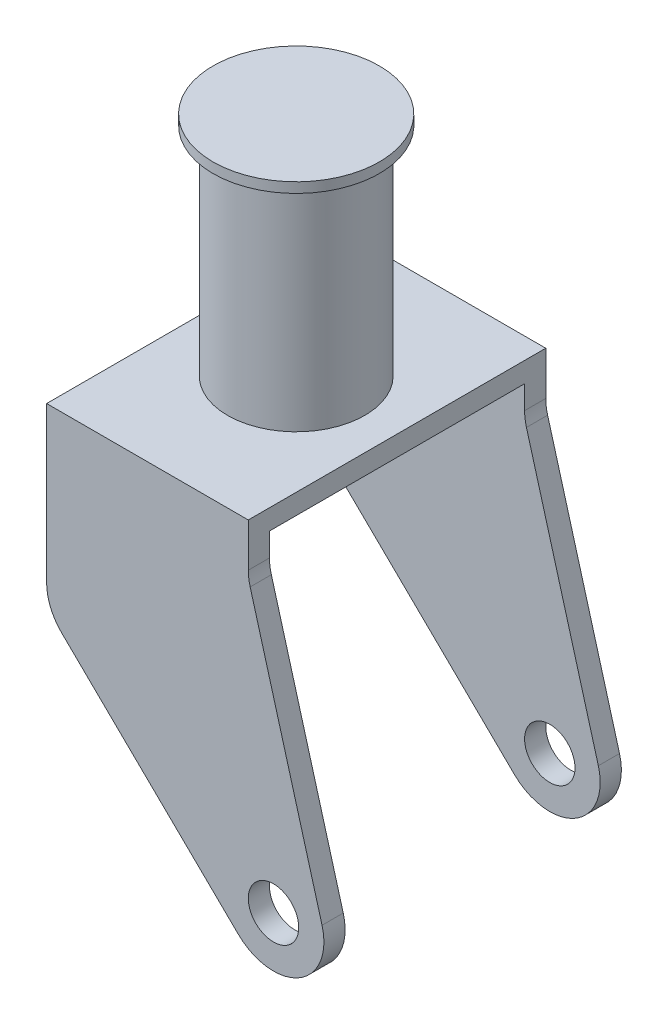
SolidWorks part; units mm, degrees
ref_plane "Front Plane" through (0, 0, 0) normal (0, 0, 1) x (1, 0, 0)
ref_plane "Top Plane" through (0, 0, 0) normal (0, 1, 0) x (1, 0, 0)
ref_plane "Right Plane" through (0, 0, 0) normal (1, 0, 0) x (0, 0, -1)
sketch "Sketch1" plane through (0, 0, 0) normal (0, 0, 1) x (1, 0, 0)
  line L0 (0, 38.1873) -> (0, -28.2019) construction
  line L1 (0, 57.15) -> (20.955, 57.15)
  line L2 (20.955, 57.15) -> (20.955, 54.61)
  line L3 (20.955, 54.61) -> (17.272, 54.61)
  line L4 (17.272, 54.61) -> (17.272, 0)
  line L5 (17.272, 0) -> (0, 0)
  line L6 (0, 0) -> (0, 57.15)
  point P5 (19.1135, 54.61)
  dimension "D1" = 34.544
  dimension "D2" = 41.91
  dimension "D3" = 2.54
  dimension "D4" = 57.15
revolve "Revolve1" add sketch "Sketch1" angle 360 about L0
sketch "Sketch2" plane through (0, 0, 0) normal (0, 0, 1) x (1, 0, 0)
  line L0 (-25.4, 0) -> (25.4, 0)
  line L1 (25.4, 0) -> (25.4, -10.9573)
  line L2 (25.8694, -14.3783) -> (43.9806, -79.129)
  line L3 (22.8729, -91.6323) -> (-21.5771, -48.1866)
  line L4 (-25.4, -39.1043) -> (-25.4, 0)
  line L5 (0, 92.2723) -> (0, -104.1278) construction
  arc A0 (43.9806, -79.129) -> (22.8729, -91.6323) centre (31.75, -82.55) cw
  arc A1 (-21.5771, -48.1866) -> (-25.4, -39.1043) centre (-12.7, -39.1043) cw
  arc A2 (25.4, -10.9573) -> (25.8694, -14.3783) centre (38.1, -10.9573) ccw
  point P3 (38.8451, -84.8071)
  point P13 (-25.4, -44.45)
  point P16 (25.4, -12.7)
  dimension "D4" = 12.7
  dimension "D5" = 12.7
  dimension "D6" = 12.7
  dimension "D1" = 50.8
  dimension "D2" = 12.7
  dimension "D3" = 44.45
  dimension "D7" = 31.75
  dimension "D8" = 82.55
extrude "Boss-Extrude1" add sketch "Sketch2" along normal blind 37.465 and the other way blind 37.465
sketch "Sketch3" plane through (-25.4, 0, 0) normal (-1, 0, 0) x (0, 0, 1)
  line L0 (0, 94.0247) -> (0, -129.8028) construction
  line L1 (-32.131, -5.08) -> (32.131, -5.08)
  line L2 (-32.131, -5.08) -> (-32.131, -115.7283)
  line L3 (-32.131, -115.7283) -> (32.131, -115.7283)
  line L4 (32.131, -5.08) -> (32.131, -115.7283)
  line L6 (-37.465, 0) -> (37.465, 0) construction
  dimension "D1" = 64.262
  dimension "D2" = 5.08
extrude "Cut-Extrude1" cut sketch "Sketch3" against normal blind 109.601 and the other way blind 55.118
sketch "Sketch4" plane through (0, 0, 37.465) normal (0, 0, 1) x (1, 0, 0)
  circle A0 centre (31.75, -82.55) radius 6.35
  dimension "D1" = 12.7
extrude "Cut-Extrude2" cut sketch "Sketch4" against normal blind 109.601
